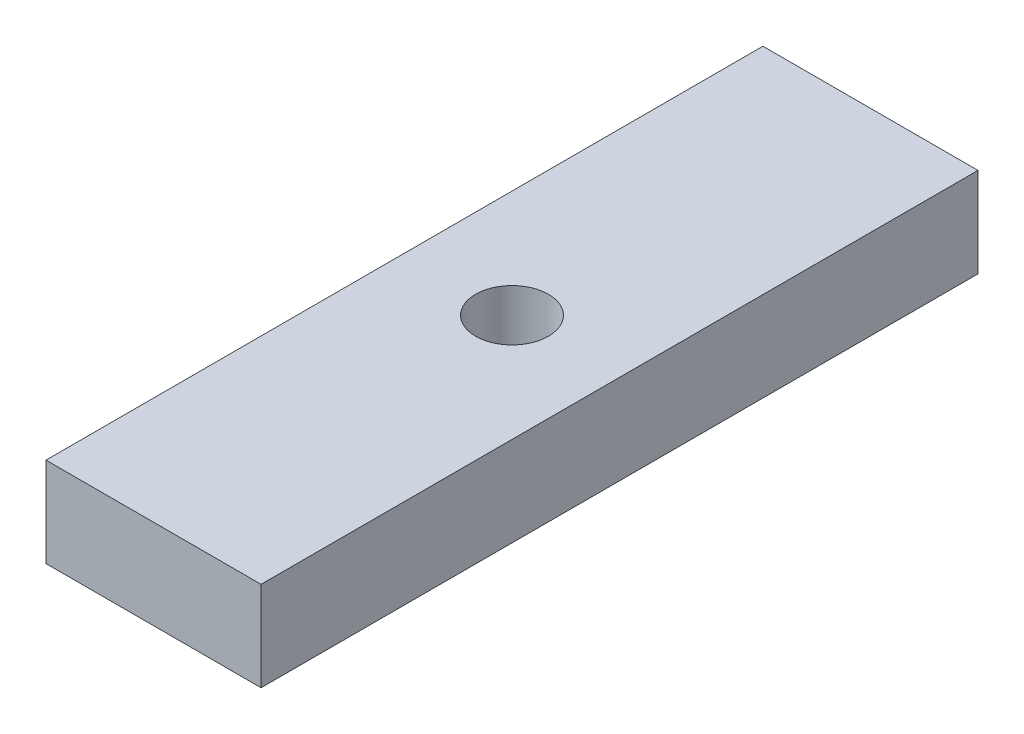
SolidWorks part; units mm, degrees
ref_plane "Front Plane" through (0, 0, 0) normal (0, 0, 1) x (1, 0, 0)
ref_plane "Top Plane" through (0, 0, 0) normal (0, 1, 0) x (1, 0, 0)
ref_plane "Right Plane" through (0, 0, 0) normal (1, 0, 0) x (0, 0, -1)
sketch "Sketch1" plane through (0, 0, 0) normal (0, 0, 1) x (1, 0, 0)
  line L1 (-38.1, -15.875) -> (38.1, -15.875)
  line L2 (-38.1, -15.875) -> (-38.1, 15.875)
  line L3 (-38.1, 15.875) -> (38.1, 15.875)
  line L4 (38.1, -15.875) -> (38.1, 15.875)
  line L5 (-38.1, -15.875) -> (38.1, 15.875) construction
  line L6 (-38.1, 15.875) -> (38.1, -15.875) construction
  point P0 (0, 0)
  dimension "D1" = 31.75
  dimension "D2" = 76.2
extrude "Boss-Extrude1" add sketch "Sketch1" along normal mid plane 254
sketch "Sketch2" plane through (0, 15.875, 0) normal (0, 1, 0) x (1, 0, 0)
  line L0 (-38.1, 0) -> (38.1, 0) construction
  line L1 (-38.1, -127) -> (-38.1, 127) construction
  line L2 (38.1, -127) -> (38.1, 127) construction
  point P6 (0, 0)
hole_wizard "1 Clearance Hole1" positions "Sketch4" profile "Sketch5" hole size "1" standard "Ansi Inch"
sketch "Sketch4" plane through (0, 15.875, 0) normal (0, 1, 0) x (-1, 0, 0)
  point P1 (0, 0)
sketch "Sketch5" plane through (0, 15.875, 0) normal (1, 0, 0) x (0, 0, 1)
  line L0 (0, 0) -> (0, 31.753)
  line L1 (0, 31.753) -> (12.8981, 24.003)
  line L2 (12.8981, 24.003) -> (12.8981, 0)
  line L5 (12.8981, 0) -> (0, 0)
  line L10 (0, 31.753) -> (-12.8981, 24.003) construction
  line L11 (0, -6.35) -> (0, 107.95) construction
  dimension "Hole Dia." = 25.7962
  dimension "Hole Depth" = 24.003
  dimension "Drill Angle" = 118
